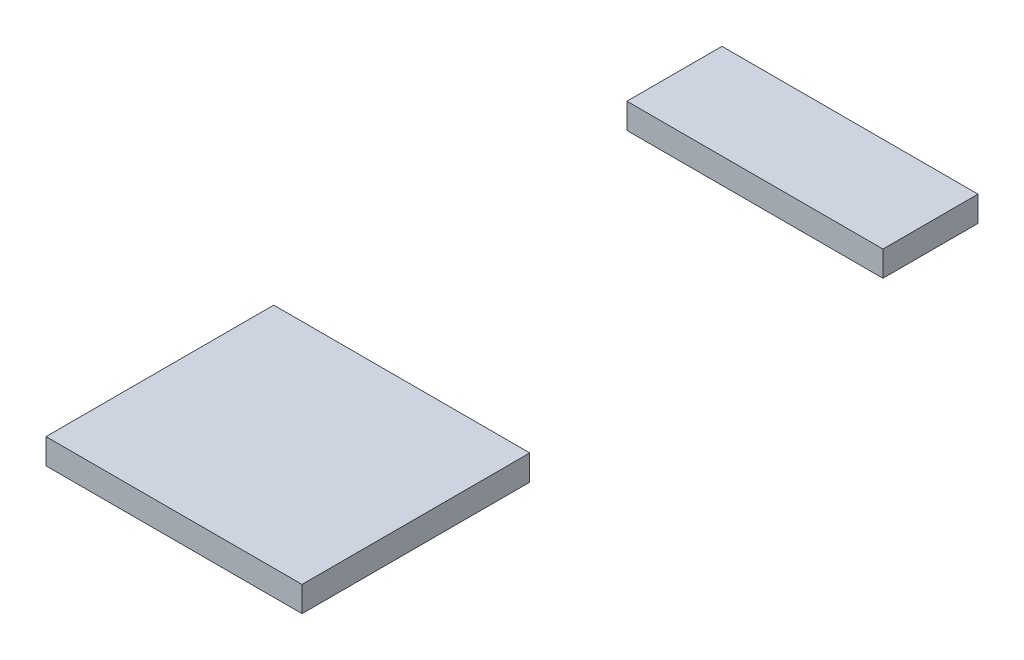
SolidWorks part; units mm, degrees
ref_plane "Front Plane" through (0, 0, 0) normal (0, 0, 1) x (1, 0, 0)
ref_plane "Top Plane" through (0, 0, 0) normal (0, 1, 0) x (1, 0, 0)
ref_plane "Right Plane" through (0, 0, 0) normal (1, 0, 0) x (0, 0, -1)
sketch "Sketch1" plane through (0, 0, 0) normal (0, 1, 0) x (1, 0, 0)
  line L0 (30.3, 68.25) -> (0, 68.25) construction
  line L1 (0, 0) -> (30.3, 0)
  line L2 (0, 0) -> (0, 80) construction
  line L3 (0, 80) -> (30.3, 80)
  line L4 (30.3, 0) -> (30.3, 80) construction
  line L5 (30.3, 27.45) -> (0, 27.45) construction
  line L6 (3.5, 68.25) -> (30.3, 68.25) construction
  line L7 (30.3, 27.45) -> (3.5, 27.45) construction
  line L8 (30.3, 68.75) -> (0, 68.75)
  line L9 (0, 26.95) -> (30.3, 26.95)
  line L10 (15.15, 27.45) -> (15.15, 26.95) construction
  line L11 (15.15, 68.25) -> (15.15, 68.75) construction
  line L12 (0, 80) -> (0, 68.75)
  line L14 (30.3, 80) -> (30.3, 68.75)
  line L15 (30.3, 26.95) -> (30.3, 0)
  line L16 (0, 26.95) -> (0, 0)
  dimension "D1" = 0.5
sketch "Sketch2" plane through (0, 0, 0) normal (0, 0, 1) x (1, 0, 0)
  line L1 (0, -3) -> (30.3, -3)
  line L2 (0, -3) -> (0, 0)
  line L3 (0, 0) -> (30.3, 0)
  line L4 (30.3, -3) -> (30.3, 0)
extrude "Boss-Extrude1" add sketch "Sketch1" against normal up to vertex (3 mm away) up to point (0, -3, 0)
